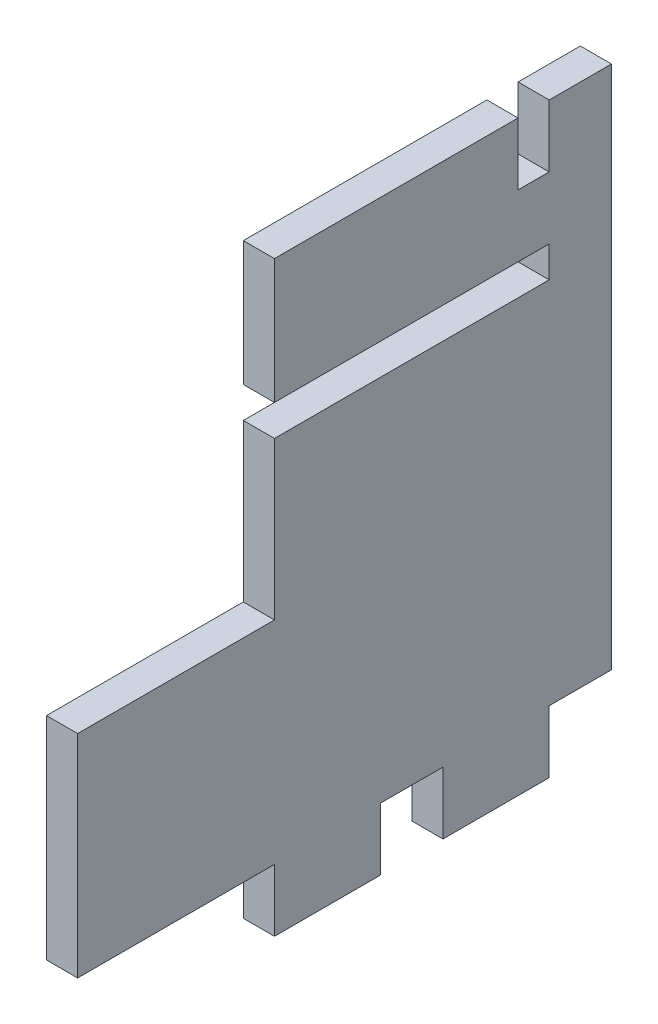
SolidWorks part; units mm, degrees
material "Acrylic (Medium-high impact)"
ref_plane "Front Plane" through (0, 0, 0) normal (0, 0, 1) x (1, 0, 0)
ref_plane "Top Plane" through (0, 0, 0) normal (0, 1, 0) x (1, 0, 0)
ref_plane "Right Plane" through (0, 0, 0) normal (1, 0, 0) x (0, 0, -1)
sketch "Sketch1" plane through (0, 0, 0) normal (1, 0, 0) x (0, 0, -1)
  line L0 (-17.175, -15.621) -> (-14, -15.621)
  line L1 (-14, 21.971) -> (14, 21.971)
  line L2 (-14, 21.971) -> (-14, -21.971)
  line L3 (-14, -21.971) -> (14, -21.971)
  line L4 (14, 21.971) -> (14, -21.971)
  line L5 (-14, 21.971) -> (14, -21.971) construction
  line L6 (-14, -21.971) -> (14, 21.971) construction
  line L15 (14, 21.971) -> (10.825, 21.971)
  line L16 (14, 21.971) -> (14, 9.271)
  line L17 (14, 9.271) -> (10.825, 9.271)
  line L18 (10.825, 21.971) -> (10.825, 9.271)
  line L19 (14, -2.921) -> (10.825, -2.921)
  line L20 (14, -2.921) -> (14, -15.621)
  line L21 (14, -15.621) -> (10.825, -15.621)
  line L22 (10.825, -2.921) -> (10.825, -15.621)
  line L35 (-3.175, -21.971) -> (3.175, -21.971)
  line L36 (-3.175, -21.971) -> (-3.175, -15.621)
  line L37 (-3.175, -15.621) -> (3.175, -15.621)
  line L38 (3.175, -21.971) -> (3.175, -15.621)
  line L55 (-14, 5.954) -> (-17.175, 5.954)
  line L59 (14, 21.971) -> (20.35, 21.971)
  line L60 (14, 21.971) -> (14, -21.971)
  line L61 (14, -21.971) -> (20.35, -21.971)
  line L62 (20.35, 21.971) -> (20.35, -21.971)
  line L63 (3.175, -15.621) -> (10.825, -15.621)
  line L64 (3.175, -15.621) -> (3.175, -21.971)
  line L65 (3.175, -21.971) -> (10.825, -21.971)
  line L66 (10.825, -15.621) -> (10.825, -21.971)
  line L67 (14, -15.621) -> (20.35, -15.621)
  line L68 (14, -15.621) -> (14, -21.971)
  line L69 (14, -21.971) -> (20.35, -21.971)
  line L70 (20.35, -15.621) -> (20.35, -21.971)
  line L71 (20.35, 25.146) -> (-14, 25.146)
  line L72 (20.35, 25.146) -> (20.35, 37.846)
  line L73 (20.35, 37.846) -> (-14, 37.846)
  line L74 (-14, 25.146) -> (-14, 37.846)
  line L83 (20.35, 21.971) -> (14, 21.971)
  line L84 (20.35, 21.971) -> (20.35, 25.146)
  line L85 (20.35, 25.146) -> (14, 25.146)
  line L86 (14, 21.971) -> (14, 25.146)
  line L87 (14, 37.846) -> (10.825, 37.846)
  line L88 (14, 37.846) -> (14, 31.496)
  line L89 (14, 31.496) -> (10.825, 31.496)
  line L90 (10.825, 37.846) -> (10.825, 31.496)
  line L91 (-17.175, 5.954) -> (-34.0582, 5.954)
  line L92 (-17.175, 5.954) -> (-17.175, -15.621)
  line L93 (-17.175, -15.621) -> (-34.0582, -15.621)
  line L94 (-34.0582, 5.954) -> (-34.0582, -15.621)
  point P0 (0, 0)
  point P27 (0, -15.621)
  dimension "D1" = 28
  dimension "D8" = 6.35
  dimension "D5" = 12.7
  dimension "D6" = 6.35
  dimension "D3" = 12.7
  dimension "D4" = 3.175
  dimension "D12" = 6.35
  dimension "D11" = 12.7
  dimension "D7" = 3.175
  dimension "D9" = 6.35
  dimension "D14" = 16.8832
  dimension "D2" = 37.592
  dimension "D10" = 21.575
extrude "Boss-Extrude1" add sketch "Sketch1" along normal blind 3.175
equation "\"bottomThickness\"= .25in"
equation "\"wallThickness\"= .125in"
equation "\"D7@Sketch1\"=\"wallThickness\""
equation "\"D6@Sketch1\"=\"bottomThickness\""
equation "\"D4@Sketch1\"=\"wallThickness\""
equation "\"D1@Boss-Extrude1\"=\"wallThickness\""
